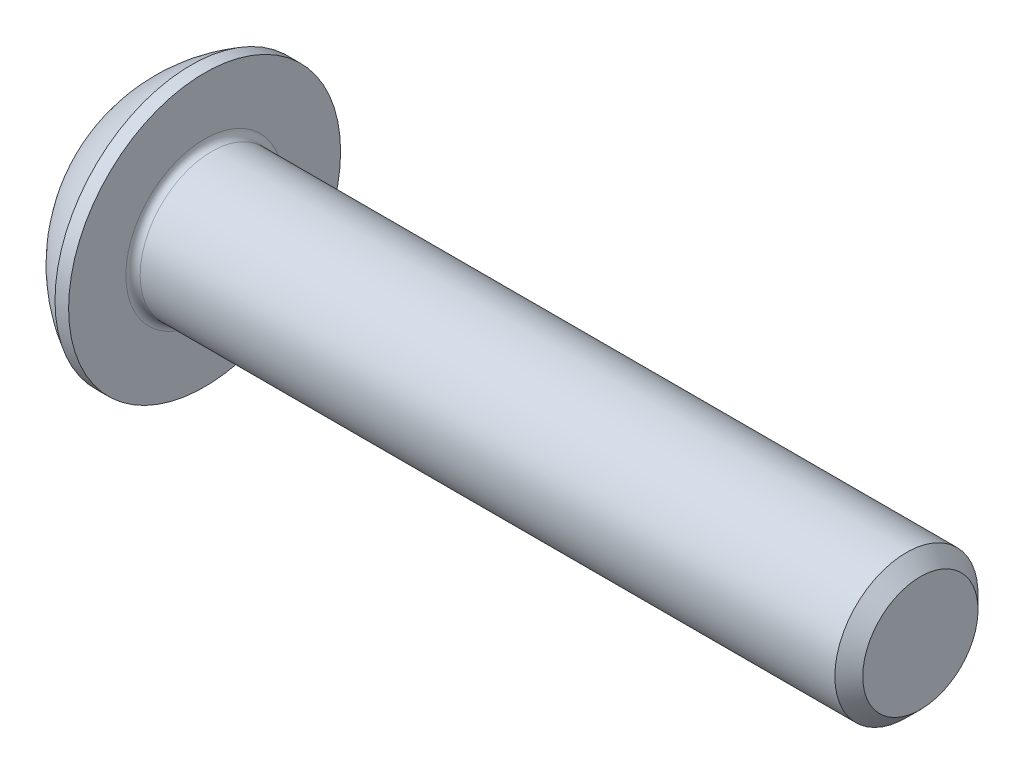
SolidWorks part; units mm, degrees
ref_plane "Plane1" through (0, 0, 0) normal (0, 0, 1) x (1, 0, 0)
ref_plane "Plane2" through (0, 0, 0) normal (0, 1, 0) x (1, 0, 0)
ref_plane "Plane3" through (0, 0, 0) normal (1, 0, 0) x (0, 0, -1)
sketch "BodySke" plane through (0, 0, 0) normal (0, 0, 1) x (1, 0, 0)
  line L0 (22.2, 0) -> (22.2, 1.61)
  line L1 (21.81, 2) -> (2.2, 2)
  line L2 (2.2, 2) -> (2.2, 3.8)
  line L3 (2.2, 3.8) -> (1.82, 3.8)
  line L4 (0, 0) -> (101.6, 0) construction
  line L5 (2.2, -3.8) -> (1.82, -3.8) construction
  line L6 (55.6768, -2) -> (2.2, -2) construction
  line L7 (22.2, 0) -> (0, 0)
  line L8 (0, 1.9) -> (0, -1.9) construction
  line L9 (0, 0) -> (0, 1.9)
  line L10 (22.2, 1.61) -> (21.81, 2)
  line L11 (22.2, -1.61) -> (21.81, -2) construction
  line L12 (2.9, 9.525) -> (2.9, -2) construction
  line L13 (6.2, 9.525) -> (6.2, -2) construction
  arc A1 (0, 1.9) -> (1.82, 3.8) centre (3.8853, 0) cw
  dimension "Diameter" = 4
  dimension "Length" = 20
  dimension "Head_dia" = 7.6
  dimension "D1" = 3.8
  dimension "Head_ht" = 2.2
  dimension "Head_side_ht" = 0.38
  dimension "Minor_dia" = 3.22
  dimension "Body_ch_ang" = 45
  dimension "Advance" = 0.7
  dimension "Thread_nom" = 16
revolve "BaseBody" add sketch "BodySke" angle 360 about L4
cosmetic thread "ThreadCosmetic" [suppressed] parameters "Thread_length"=16, "Thread_minor"=3.22
fillet "Fillet1" radius 0.2 1 edges at (2.2, 0, 2)
sketch "Sketch2" plane through (0, 0, 0) normal (0, 0, 1) x (1, 0, 0)
  line L0 (0, 1.25) -> (1.3, 1.25)
  line L1 (1.3, 1.25) -> (2.0217, 0)
  line L3 (2.0217, 0) -> (0, 0)
  line L4 (0, 0) -> (0, 1.25)
  line L5 (0, -1.25) -> (1.3, -1.25) construction
  line L6 (0, 0) -> (47.625, 0) construction
  dimension "D2" = 60
  dimension "PreBroach_depth" = 1.3
  dimension "PreBroach_dia" = 2.5
revolve "PreBroach" cut sketch "Sketch2" angle 360 about L6
sketch "Sketch3" plane through (0, 0, 0) normal (1, 0, 0) x (0, 0, -1)
  line L0 (-1.25, -0.7217) -> (-1.25, 0.7217)
  line L1 (-1.25, 0.7217) -> (0, 1.4434)
  line L2 (0, 1.4434) -> (1.25, 0.7217)
  line L3 (1.25, 0.7217) -> (1.25, -0.7217)
  line L4 (1.25, -0.7217) -> (0, -1.4434)
  line L5 (0, -1.4434) -> (-1.25, -0.7217)
  dimension "Hex_size" = 2.5
  dimension "D3" = 2.5
  dimension "D1" = 1.25
  dimension "D2" = 1.25
extrude "Hex" cut sketch "Sketch3" along normal blind 1.3
sketch "ThdSchSke" plane through (0, 0, 0) normal (0, 0, 1) x (1, 0, 0)
  line L0 (6.2, -1.61) -> (5.9269, -2)
  line L1 (6.2, -1.61) -> (6.4731, -2)
  line L2 (6.4731, -2) -> (6.4731, -2.5)
  line L3 (-3.175, 0) -> (5.1513, 0) construction
  line L5 (6.4731, -2.5) -> (5.9269, -2.5)
  line L6 (5.9269, -2.5) -> (5.9269, -2)
  dimension "Diameter" = 4
  dimension "Thread_minor" = 3.22
  dimension "SideAngle" = 55
  dimension "VeeAngle" = 70
  dimension "Overcut" = 5
  dimension "Start" = 6.2
revolve "ThreadSchematic" [suppressed] cut sketch "ThdSchSke" angle 360 about L3
pattern_linear "ThdSchPat" [suppressed]
equation "\"D1@BodySke\" = \"Head_dia@BodySke\" * .5"
equation "\"Thread_minor@ThreadCosmetic\" = \"Minor_dia@BodySke\""
equation "\"D1@Sketch3\" = \"Hex_size@Sketch3\" / 2"
equation "\"D2@Sketch3\" = \"D1@Sketch3\""
equation "\"D3@Sketch3\" = \"Hex_size@Sketch3\""
equation "\"Thread_length@ThreadCosmetic\" = ((sgn( (\"Length@BodySke\" - \"Advance@BodySke\" * 2.0) - \"Thread_nom@BodySke\" )-1)*( (\"Length@BodySke\" - \"Advance@BodySke\" * 2.0) - \"Thread_nom@BodySke\" ))/-2+ \"Thread_nom@BodySke\""
equation "\"Thread_minor@ThdSchSke\" = \"Minor_dia@BodySke\""
equation "\"Diameter@ThdSchSke\" = \"Diameter@BodySke\""
equation "\"Overcut@ThdSchSke\" = \"Diameter@BodySke\" * 1.25"
equation "\"Start@ThdSchSke\" = \"Head_ht@BodySke\" + \"Length@BodySke\" - \"Thread_length@ThreadCosmetic\"  '---Non-countersunk---"
equation "\"Num_threads@ThdSchPat\" = int( \"Thread_length@ThreadCosmetic\" / \"Advance@BodySke\" + 0.999 )  + 1"
equation "\"Advance@ThdSchPat\" = \"Thread_length@ThreadCosmetic\" /  (\"Num_threads@ThdSchPat\" - 1) 'relax it"
equation "\"Num_threads@ThdSchPat\" = \"Num_threads@ThdSchPat\" - sgn( \"Num_threads@ThdSchPat\" - 1) '---chamfered tips only---"
